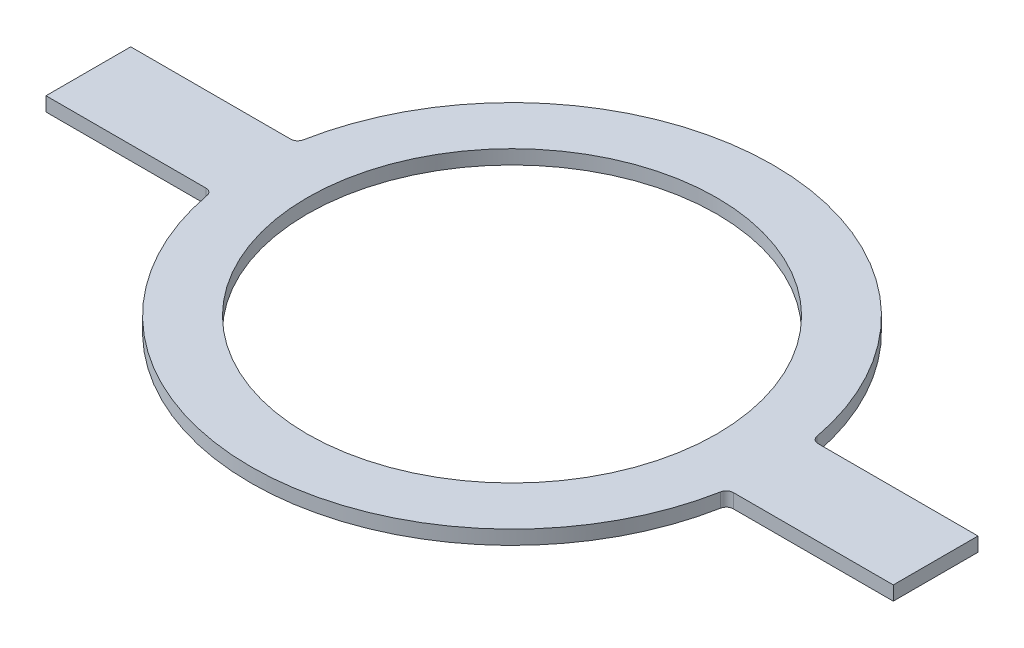
SolidWorks part; units mm, degrees
material "6061-T6 (SS)"
ref_plane "Front Plane" through (0, 0, 0) normal (0, 0, 1) x (1, 0, 0)
ref_plane "Top Plane" through (0, 0, 0) normal (0, 1, 0) x (1, 0, 0)
ref_plane "Right Plane" through (0, 0, 0) normal (1, 0, 0) x (0, 0, -1)
sketch "Sketch1" plane through (0, 0, 0) normal (0, 1, 0) x (1, 0, 0)
  line L0 (115.9201, 19.05) -> (190.5, 19.05)
  line L1 (-190.5, 19.05) -> (-115.9201, 19.05)
  line L2 (-190.5, 19.05) -> (-190.5, -19.05)
  line L3 (-190.5, -19.05) -> (-115.9201, -19.05)
  line L4 (190.5, 19.05) -> (190.5, -19.05)
  line L5 (-190.5, 19.05) -> (190.5, -19.05) construction
  line L6 (-190.5, -19.05) -> (190.5, 19.05) construction
  line L7 (115.9201, -19.05) -> (190.5, -19.05)
  circle A0 centre (0, 0) radius 92.075
  arc A1 (-115.9201, -19.05) -> (115.9201, -19.05) centre (0, 0) ccw
  arc A2 (115.9201, 19.05) -> (-115.9201, 19.05) centre (0, 0) ccw
  point P0 (0, 0)
  dimension "D3" = 184.15
  dimension "D4" = 25.4
  dimension "D1" = 381
  dimension "D2" = 38.1
extrude "Boss-Extrude1" add sketch "Sketch1" along normal blind 6.35
fillet "Fillet1" radius 3.175 4 edges at (-115.9201, 3.175, -19.05) (115.9201, 3.175, -19.05) (115.9201, 3.175, 19.05) (-115.9201, 3.175, 19.05)
